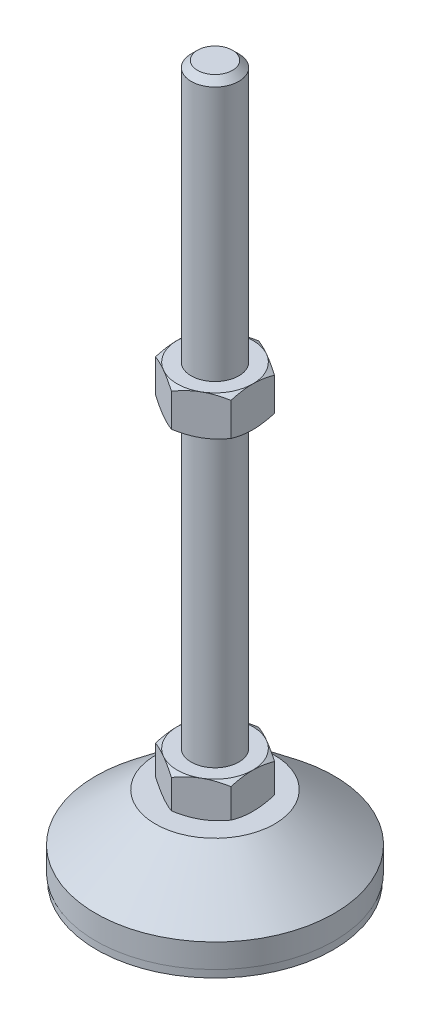
SolidWorks part; units mm, degrees
ref_plane "Спереди" through (0, 0, 0) normal (0, 0, 1) x (1, 0, 0)
ref_plane "Сверху" through (0, 0, 0) normal (0, 1, 0) x (1, 0, 0)
ref_plane "Справа" through (0, 0, 0) normal (1, 0, 0) x (0, 0, -1)
sketch "Эскиз1" plane through (0, 0, 0) normal (0, 0, 1) x (1, 0, 0)
  line L0 (0, 0) -> (-29.8, 0)
  line L1 (-29.8, 0) -> (-29.8, 2)
  line L2 (-29.8, 2) -> (-30, 2)
  line L3 (-30, 2) -> (-30, 8)
  line L4 (-30, 8) -> (-15, 20)
  line L5 (-15, 20) -> (-6, 20)
  line L12 (-6, 29) -> (-6, 177.4)
  line L13 (-6, 177.4) -> (-4.4, 179)
  line L14 (-4.4, 179) -> (0, 179)
  line L15 (0, 179) -> (0, 0) construction
  line L16 (-6, 20) -> (0, 20) construction
  line L17 (0, 0) -> (0, 179)
  line L18 (0, 0) -> (0, -7.9595) construction
  line L19 (-6, 29) -> (-6, 20)
  point P8 (-6, 103.2)
  point P23 (-10.5, 20)
  dimension "D1" = 12
  dimension "D2" = 20
  dimension "D3" = 9
  dimension "D4" = 60
  dimension "D5" = 6
  dimension "D6" = 1.6
  dimension "D7" = 45
  dimension "D8" = 30
  dimension "D9" = 2
  dimension "D10" = 150
  dimension "D11" = 6
  dimension "D12" = 0.2
revolve "Повернуть1" add sketch "Эскиз1" angle 360 about L17
sketch "Эскиз2" plane through (0, 20, 0) normal (0, 1, 0) x (1, 0, 0)
  line L1 (0, 10.9697) -> (-9.5, 5.4848)
  line L2 (-9.5, 5.4848) -> (-9.5, -5.4848)
  line L3 (-9.5, -5.4848) -> (0, -10.9697)
  line L4 (0, -10.9697) -> (9.5, -5.4848)
  line L5 (9.5, -5.4848) -> (9.5, 5.4848)
  line L6 (9.5, 5.4848) -> (0, 10.9697)
  circle A0 centre (0, 0) radius 9.5 construction
  dimension "D1" = 19
extrude "Бобышка-Вытянуть1" add sketch "Эскиз2" along normal up to vertex (9 mm away) up to point (-6, 29, 0)
ref_plane "Плоскость1" through (0, 103.2, 0) normal (0, 1, 0) x (1, 0, 0)
sketch "Эскиз3" plane through (0, 103.2, 0) normal (0, 1, 0) x (1, 0, 0)
  line L6 (9.5, 5.4848) -> (0, 10.9697)
  line L7 (0, 10.9697) -> (-9.5, 5.4848)
  line L8 (-9.5, 5.4848) -> (-9.5, -5.4848)
  line L9 (-9.5, -5.4848) -> (0, -10.9697)
  line L10 (0, -10.9697) -> (9.5, -5.4848)
  line L11 (9.5, -5.4848) -> (9.5, 5.4848)
  line L12 (9.5, 5.4848) -> (0, 10.9697)
  line L13 (0, 10.9697) -> (-9.5, 5.4848)
  line L14 (-9.5, 5.4848) -> (-9.5, -5.4848)
  line L15 (-9.5, -5.4848) -> (0, -10.9697)
  line L16 (0, -10.9697) -> (9.5, -5.4848)
  line L17 (9.5, -5.4848) -> (9.5, 5.4848)
  dimension "D1" = 0
extrude "Бобышка-Вытянуть2" add sketch "Эскиз3" along normal blind 10
sketch "Эскиз4" plane through (0, 0, 0) normal (0, 0, 1) x (1, 0, 0)
  line L0 (-9.5, 113.2) -> (-18.1603, 108.2)
  line L1 (-18.1603, 108.2) -> (-18.1603, 113.2)
  line L2 (-18.1603, 113.2) -> (-9.5, 113.2)
  line L3 (-18.1603, 108.2) -> (-9.5, 103.2)
  line L4 (50, 103.2) -> (-50, 103.2) construction
  line L5 (-9.5, 103.2) -> (-18.1603, 103.2)
  line L6 (-18.1603, 103.2) -> (-18.1603, 108.2)
  line L7 (-9.5, 113.2) -> (-9.5, 103.2) construction
  line L8 (-9.5, 29) -> (-17.2942, 29)
  line L9 (-17.2942, 29) -> (-17.2942, 24.5)
  line L10 (-17.2942, 24.5) -> (-9.5, 29)
  line L11 (-9.5, 20) -> (-17.2942, 24.5)
  line L12 (-17.2942, 24.5) -> (-17.2942, 20)
  line L13 (-17.2942, 20) -> (-9.5, 20)
  line L14 (0, 179) -> (0, 96.3793) construction
  dimension "D1" = 30
  dimension "D2" = 30
revolve "Вырез-Повернуть2" cut sketch "Эскиз4" angle 360 about L14
